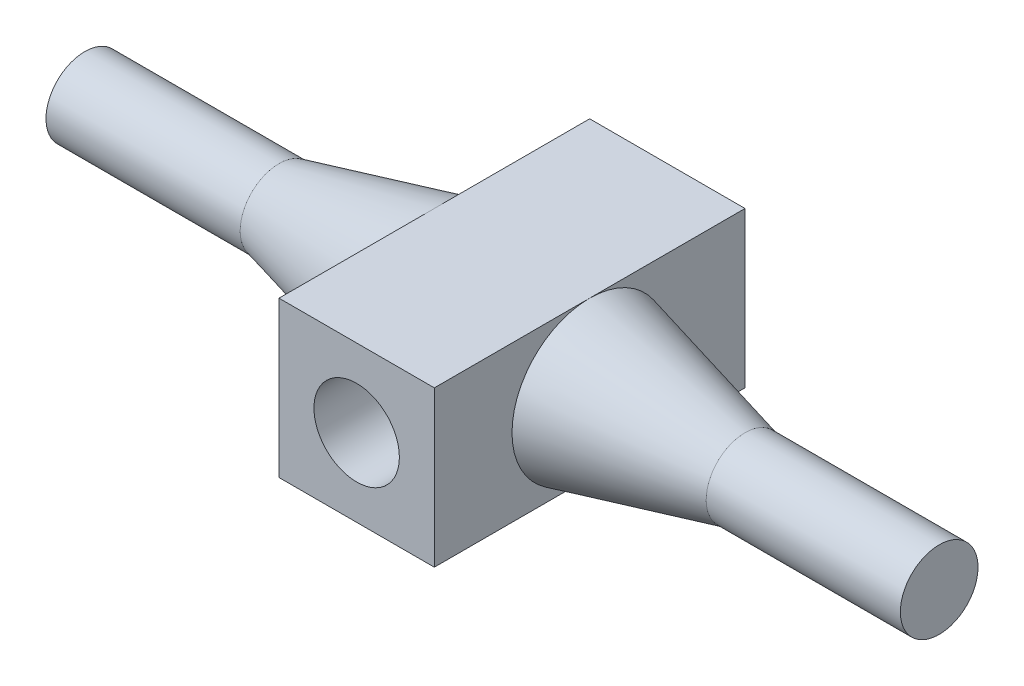
SolidWorks part; units mm, degrees
ref_plane "Front Plane" through (0, 0, 0) normal (0, 0, 1) x (1, 0, 0)
ref_plane "Top Plane" through (0, 0, 0) normal (0, 1, 0) x (1, 0, 0)
ref_plane "Right Plane" through (0, 0, 0) normal (1, 0, 0) x (0, 0, -1)
sketch "Sketch1" plane through (0, 0, 0) normal (0, 0, 1) x (1, 0, 0)
  line L1 (1, -1) -> (-1, -1)
  line L2 (1, -1) -> (1, 1)
  line L3 (1, 1) -> (-1, 1)
  line L4 (-1, -1) -> (-1, 1)
  line L5 (1, -1) -> (-1, 1) construction
  line L6 (1, 1) -> (-1, -1) construction
  circle A0 centre (0, 0) radius 0.55
  dimension "D1" = 1.1
  dimension "D2" = 2
  dimension "D3" = 2
extrude "Boss-Extrude1" add sketch "Sketch1" along normal blind 4
ref_plane "Plane4" through (0, 0, 2) normal (0, 0, 1) x (1, 0, 0)
sketch "草图1" plane through (0, 0, 2) normal (0, 0, 1) x (1, 0, 0)
  line L0 (1, 1) -> (1, 0)
  line L1 (0, -1000) -> (0, 49000) construction
  line L2 (-1, 0) -> (-5.5, 0)
  line L3 (-1, 1) -> (-1, -1) construction
  line L4 (-1, 1) -> (-1, 0)
  line L5 (-3, 0.5) -> (-1, 1)
  line L6 (-5.5, 0) -> (-5.5, 0.5)
  line L7 (-5.5, 0.5) -> (-3, 0.5)
  line L8 (3, 0.5) -> (1, 1)
  line L9 (5.5, 0.5) -> (3, 0.5)
  line L10 (5.5, 0) -> (5.5, 0.5)
  line L11 (1, 0) -> (5.5, 0)
revolve "旋转1" add sketch "草图1" angle 360 about L2
